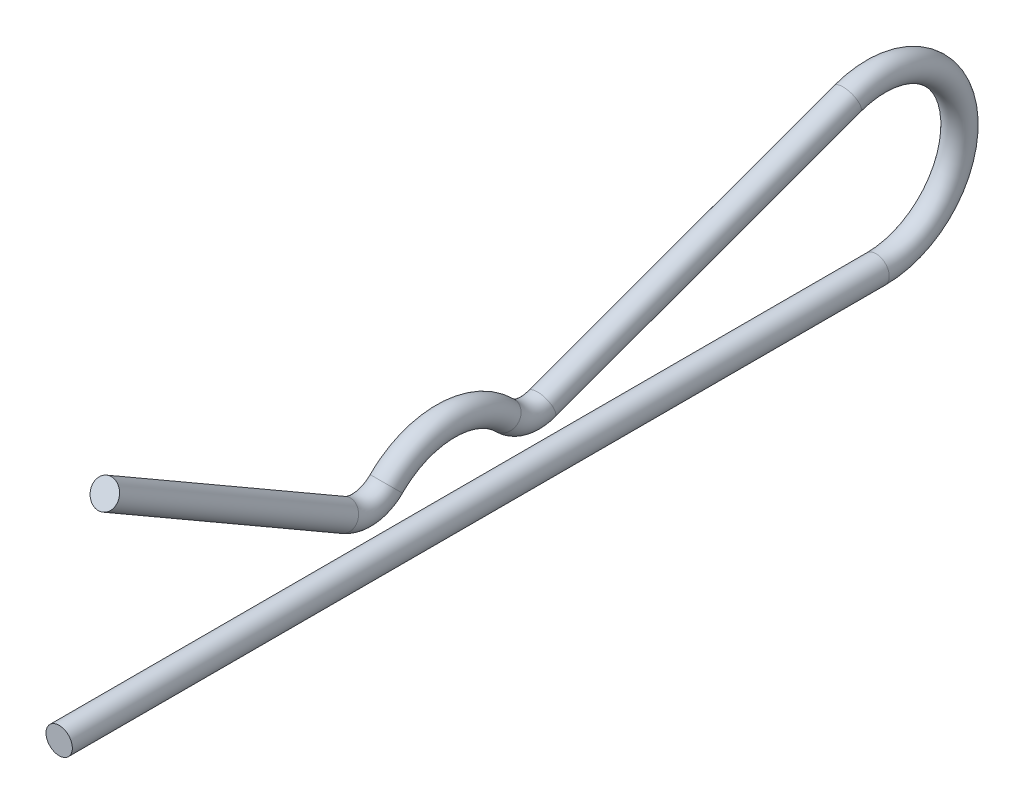
SolidWorks part; units mm, degrees
ref_plane "Front" through (0, 0, 0) normal (0, 0, 1) x (1, 0, 0)
ref_plane "Top" through (0, 0, 0) normal (0, 1, 0) x (1, 0, 0)
ref_plane "Right" through (0, 0, 0) normal (1, 0, 0) x (0, 0, -1)
sketch "Sketch1" plane through (0, 0, 0) normal (0, 0, 1) x (1, 0, 0)
  circle A0 centre (0, 0) radius 0.5953
sketch "Sketch2" plane through (0, 0, 0) normal (1, 0, 0) x (0, 0, -1)
  line L0 (0, 0) -> (36.9094, 0)
  line L1 (13.6558, 3.7703) -> (21.2692, 3.7703) construction
  line L2 (41.275, 0) -> (41.275, 3.7703) construction
  line L3 (41.275, 3.7703) -> (40.6797, 3.7703) construction
  line L5 (41.275, 0) -> (0, 0) construction
  line L6 (12.8621, 2.3955) -> (2.0637, 8.6299)
  line L7 (17.4625, 3.7703) -> (17.4625, 0) construction
  line L13 (35.6178, 7.3125) -> (21.813, 2.2789)
  circle A0 centre (36.9094, 3.7703) radius 3.175 construction
  arc A1 (20.1413, 2.6532) -> (14.7837, 2.6532) centre (17.4625, 0) ccw
  arc A6 (14.7837, 2.6532) -> (12.8621, 2.3955) centre (13.6558, 3.7703) cw
  arc A8 (21.813, 2.2789) -> (20.1413, 2.6532) centre (21.2692, 3.7703) cw
  arc A9 (36.9094, 0) -> (35.6178, 7.3125) centre (36.9094, 3.7703) ccw
  dimension "D1" = 1.5875
  dimension "D2" = 17.4625
  dimension "D5" = 2.0638
  dimension "D9" = 30
  dimension "D11" = 0.5953
  dimension "D3" = 0.5953
sweep "Sweep1" add profiles "Sketch1" path "Sketch2"
equation "\"D11@Sketch2\" = \"WireOD@Sketch1\"/2"
equation "\"D1@Sketch2\" = \"EyeID@Sketch2\"/4"
equation "\"D3@Sketch2\" = \"D11@Sketch2\""
equation "\"D2@Sketch2\" = (\"Length@Sketch2\"-\"EyeID@Sketch2\")/2"
equation "\"D5@Sketch2\" = \"Length@Sketch2\"*.05"
